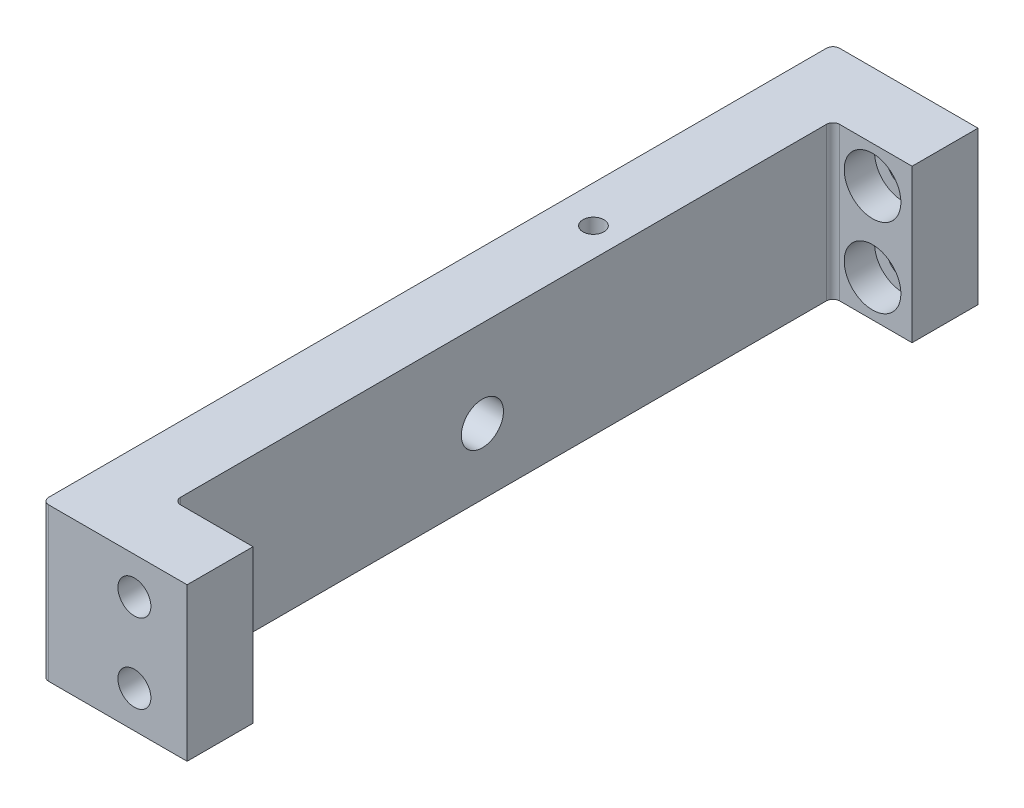
SolidWorks part; units mm, degrees
ref_plane "前视基准面" through (0, 0, 0) normal (0, 0, 1) x (1, 0, 0)
ref_plane "上视基准面" through (0, 0, 0) normal (0, 1, 0) x (1, 0, 0)
ref_plane "右视基准面" through (0, 0, 0) normal (1, 0, 0) x (0, 0, -1)
sketch "草图1" plane through (0, 0, 0) normal (0, 0, 1) x (1, 0, 0)
  line L1 (2.5, -5.8) -> (-2.5, -5.8)
  line L2 (2.5, -5.8) -> (2.5, 5.8)
  line L3 (2.5, 5.8) -> (-2.5, 5.8)
  line L4 (-2.5, -5.8) -> (-2.5, 5.8)
  line L5 (2.5, -5.8) -> (-2.5, 5.8) construction
  line L6 (2.5, 5.8) -> (-2.5, -5.8) construction
  point P0 (0, 0)
  dimension "D1" = 5
  dimension "D2" = 11.6
extrude "凸台-拉伸1" add sketch "草图1" along normal mid plane 60
sketch "草图2" plane through (2.5, 0, 0) normal (1, 0, 0) x (0, 0, -1)
  line L0 (-30, -5.8) -> (-30, 5.8)
  line L1 (-30, 5.8) -> (-25, 5.8)
  line L2 (-30, 5.8) -> (30, 5.8) construction
  line L3 (-25, 5.8) -> (-25, -5.8)
  line L4 (-30, -5.8) -> (30, -5.8) construction
  line L5 (-25, -5.8) -> (-30, -5.8)
  dimension "D1" = 5
extrude "凸台-拉伸2" add sketch "草图2" along normal blind 6
mirror "镜向1" about plane through (0, 0, 0) normal (0, 0, 1) of "凸台-拉伸2"
hole_wizard "M3 螺纹孔1" positions "草图3" profile "草图4" tap size "M3" standard "GB"
sketch "草图3" plane through (0, 0, 30) normal (0, 0, 1) x (1, 0, 0)
  line L0 (8.5, 5.8) -> (8.5, -5.8) construction
  point P0 (4.5, -3)
  point P2 (4.5, 3)
  dimension "D1" = 6
  dimension "D2" = 3
  dimension "D3" = 4
sketch "草图4" plane through (4.5, -3, 30) normal (1, 0, 0) x (0, -1, 0)
  line L0 (0, 0) -> (0, 8.2511)
  line L1 (0, 8.2511) -> (1.25, 7.5)
  line L2 (1.25, 7.5) -> (1.25, 0)
  line L5 (1.25, 0) -> (0, 0)
  line L10 (0, 8.2511) -> (-1.25, 7.5) construction
  line L11 (0, -6.35) -> (0, 107.95) construction
  dimension "螺纹孔钻头直径" = 2.5
  dimension "螺纹孔钻头深度" = 7.5
  dimension "导头角度" = 118
cosmetic thread "孔螺蚊线1" parameters "D1"=5, "D2"=3
cosmetic thread "孔螺蚊线2" parameters "D1"=5, "D2"=3
hole_wizard "打孔尺寸(%根据)内六角圆柱头螺钉的类型1" positions "草图7" profile "草图6" counterbore size "M2" standard "GB"
sketch "草图7" plane through (0, 0, -25) normal (0, 0, 1) x (1, 0, 0)
  line L0 (8.5, -5.8) -> (8.5, 5.8) construction
  point P0 (5.5, -3)
  point P2 (5.5, 3)
  dimension "D1" = 6
  dimension "D2" = 3
  dimension "D3" = 3
sketch "草图6" plane through (5.5, -3, -25) normal (1, 0, 0) x (0, -1, 0)
  line L0 (0, 0) -> (0, 8.221)
  line L1 (0, 8.221) -> (1.2, 7.5)
  line L2 (1.2, 7.5) -> (1.2, 2.3)
  line L3 (1.2, 2.3) -> (2.15, 2.3)
  line L4 (2.15, 2.3) -> (2.15, 0)
  line L5 (2.15, 0) -> (0, 0)
  line L10 (0, 8.221) -> (-1.2, 7.5) construction
  line L11 (0, -6.35) -> (0, 107.95) construction
  dimension "孔直径" = 2.4
  dimension "孔深度" = 7.5
  dimension "柱形沉头孔直径" = 4.3
  dimension "柱形沉头孔深度" = 2.3
  dimension "导头角度" = 118
fillet "圆角1" radius 0.5 4 edges at (-2.5, 0, -30) (2.5, 0, -25) (2.5, 0, 25) (-2.5, 0, 30)
hole_wizard "Ø3.2 (3.2) 直径孔1" positions "草图8" profile "草图9" hole size "Ø3.2" standard "GB"
sketch "草图8" plane through (-2.5, 0, 0) normal (-1, 0, 0) x (0, 0, 1)
  point P0 (1.6, -0.8)
sketch "草图9" plane through (-2.5, -0.8, 1.6) normal (0, 1, 0) x (0, 0, 1)
  line L0 (0, 0) -> (0, 6.1614)
  line L1 (0, 6.1614) -> (1.6, 5.2)
  line L2 (1.6, 5.2) -> (1.6, 0)
  line L5 (1.6, 0) -> (0, 0)
  line L10 (0, 6.1614) -> (-1.6, 5.2) construction
  line L11 (0, -6.35) -> (0, 107.95) construction
  dimension "孔直径" = 3.2
  dimension "孔深度" = 5.2
  dimension "导头角度" = 118
hole_wizard "M2 螺纹孔1" positions "草图10" profile "草图11" tap size "M2" standard "GB"
sketch "草图10" plane through (0, 5.8, 0) normal (0, 1, 0) x (1, 0, 0)
  point P0 (0.325, 9)
sketch "草图11" plane through (0.325, 5.8, -9) normal (1, 0, 0) x (0, 0, 1)
  line L0 (0, 0) -> (0, 5.6807)
  line L1 (0, 5.6807) -> (0.8, 5.2)
  line L2 (0.8, 5.2) -> (0.8, 0)
  line L5 (0.8, 0) -> (0, 0)
  line L10 (0, 5.6807) -> (-0.8, 5.2) construction
  line L11 (0, -6.35) -> (0, 107.95) construction
  dimension "螺纹孔钻头直径" = 1.6
  dimension "螺纹孔钻头深度" = 5.2
  dimension "导头角度" = 118
cosmetic thread "孔螺蚊线3" parameters "D1"=4, "D2"=2
